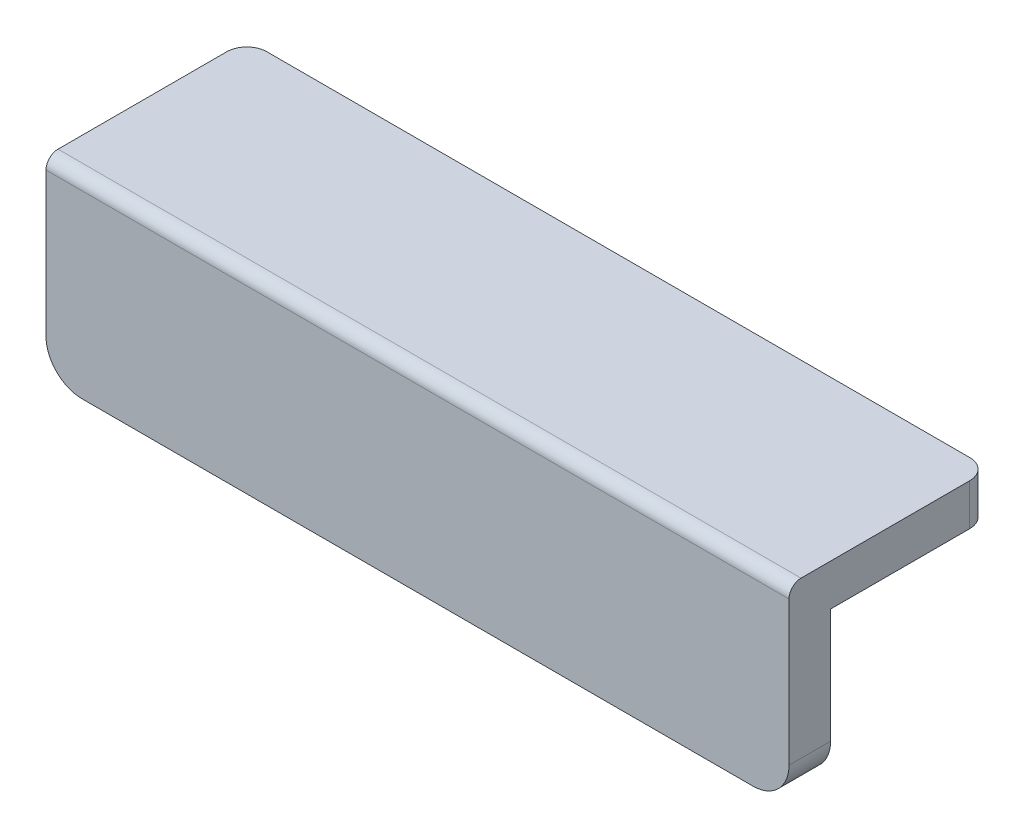
SolidWorks part; units mm, degrees
ref_plane "Front Plane" through (0, 0, 0) normal (0, 0, 1) x (1, 0, 0)
ref_plane "Top Plane" through (0, 0, 0) normal (0, 1, 0) x (1, 0, 0)
ref_plane "Right Plane" through (0, 0, 0) normal (1, 0, 0) x (0, 0, -1)
sketch "Sketch1" plane through (0, 0, 0) normal (0, 0, 1) x (1, 0, 0)
  line L1 (-46.99, -9.525) -> (46.99, -9.525)
  line L2 (-46.99, -9.525) -> (-46.99, 9.525)
  line L3 (-46.99, 9.525) -> (46.99, 9.525)
  line L4 (46.99, -9.525) -> (46.99, 9.525)
  line L5 (-46.99, -9.525) -> (46.99, 9.525) construction
  line L6 (-46.99, 9.525) -> (46.99, -9.525) construction
  point P0 (0, 0)
  dimension "D1" = 19.05
  dimension "D2" = 93.98
extrude "Boss-Extrude1" add sketch "Sketch1" along normal mid plane 5.2578
sketch "Sketch2" plane through (0, 9.525, 0) normal (0, 1, 0) x (1, 0, 0)
  line L0 (46.99, -2.6289) -> (46.99, 2.6289) construction
  line L1 (-46.99, -2.6289) -> (46.99, -2.6289)
  line L2 (-46.99, -2.6289) -> (-46.99, 22.7711)
  line L3 (-46.99, 22.7711) -> (46.99, 22.7711)
  line L4 (46.99, -2.6289) -> (46.99, 22.7711)
  dimension "D1" = 25.4
extrude "Boss-Extrude2" add sketch "Sketch2" along normal blind 5.2578
fillet "Fillet6" radius 4.572 1 edges at (-46.99, -9.525, 0)
fillet "Fillet7" radius 4.572 2 edges at (46.99, -9.525, 0)
fillet "Fillet8" radius 1.524 1 edges at (0, 14.7828, 2.6289)
fillet "Fillet9" radius 2.54 2 edges at (-46.99, 12.1539, -22.7711)
fillet "Fillet10" radius 2.54 1 edges at (46.99, 12.1539, -22.7711)
equation "\"Acrylic\"=\"Acrylic@Bumper.assembly\""
equation "\"D1@Boss-Extrude1\" = \"Acrylic\""
equation "\"D1@Boss-Extrude2\"=\"Acrylic\""
equation "\"D2@Sketch1\" = \"BumperWidth@Bumper.assembly\""
